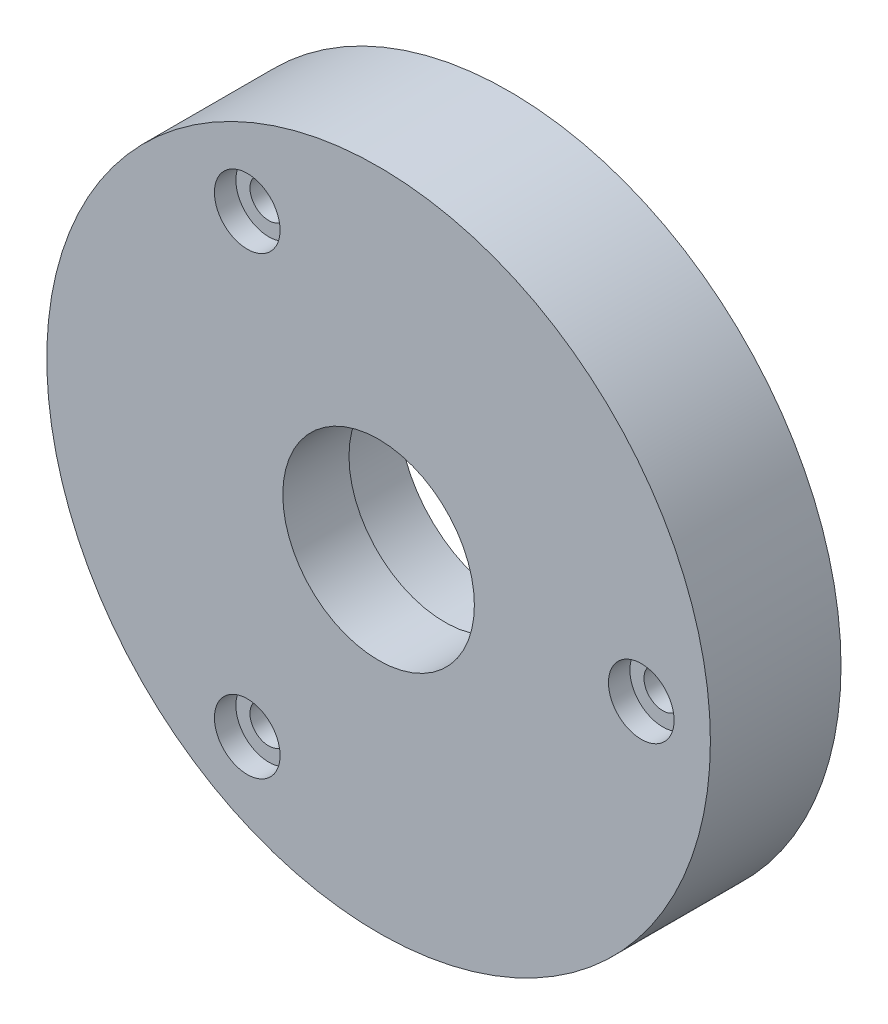
SolidWorks part; units mm, degrees
material "Alliage 1060"
ref_plane "Plan de face" through (0, 0, 0) normal (0, 0, 1) x (1, 0, 0)
ref_plane "Plan de dessus" through (0, 0, 0) normal (0, 1, 0) x (1, 0, 0)
ref_plane "Plan de droite" through (0, 0, 0) normal (1, 0, 0) x (0, 0, -1)
sketch "Esquisse1" plane through (0, 0, 0) normal (0, 0, 1) x (1, 0, 0)
  circle A2 centre (23.0123, 8.4359) radius 38.1
  circle A3 centre (23.0123, 8.4359) radius 11
  dimension "D1" = 76.2
  dimension "D2" = 22
extrude "Boss.-Extru.1" add sketch "Esquisse1" along normal blind 15
sketch "Esquisse2" plane through (0, 0, 0) normal (0, 0, -1) x (-1, 0, 0)
  circle A0 centre (-23.0123, 8.4359) radius 12.7
  dimension "D1" = 25.4
extrude "Enlèv. mat.-Extru.1" cut sketch "Esquisse2" against normal blind 7.4
sketch "Esquisse3" plane through (0, 0, 15) normal (0, 0, 1) x (1, 0, 0)
  line L0 (-15.0877, 8.4359) -> (61.1123, 8.4359) construction
  circle A0 centre (23.0123, 8.4359) radius 38.1 construction
  circle A1 centre (53.1748, 8.4359) radius 1.8
  circle A2 centre (7.931, -17.6856) radius 1.8
  circle A3 centre (7.931, 34.5574) radius 1.8
  point P7 (23.0123, 8.4359)
  point P12 (23.0123, 8.4359)
  dimension "D1" = 3.6
  dimension "D2" = 30.1625
  dimension "D3" = 3
hole_wizard "Chambrage pour vis à tête ronde bombée #61" positions "Esquisse4" profile "Esquisse5" counterbore size "#6" standard "Ansi Inch"
sketch "Esquisse4" plane through (0, 0, 15) normal (0, 0, 1) x (1, 0, 0)
  point P0 (7.931, 34.5574)
  point P3 (53.1748, 8.4359)
  point P6 (7.931, -17.6856)
sketch "Esquisse5" plane through (7.931, 34.5574, 15) normal (1, 0, 0) x (0, -1, 0)
  line L0 (0, 0) -> (0, 16.2934)
  line L1 (0, 16.2934) -> (2.1526, 15)
  line L2 (2.1526, 15) -> (2.1526, 2.4638)
  line L3 (2.1526, 2.4638) -> (3.7706, 2.4638)
  line L4 (3.7706, 2.4638) -> (3.7706, 0)
  line L5 (3.7706, 0) -> (0, 0)
  line L10 (0, 16.2934) -> (-2.1527, 15) construction
  line L11 (0, -6.35) -> (0, 107.95) construction
  dimension "Diamètre du perçage" = 4.3053
  dimension "Profondeur du perçage" = 15
  dimension "Diamètre du chambrage" = 7.5413
  dimension "Profondeur du chambrage" = 2.4638
  dimension "Angle de pointe" = 118
sketch "Esquisse6" plane through (0, 0, 0) normal (0, 0, -1) x (-1, 0, 0)
  line L0 (-23.0123, 8.4359) -> (-23.0123, 40.1859) construction
  line L1 (-23.0123, 8.4359) -> (-33.8714, -21.3994) construction
  dimension "D1" = 31.75
hole_wizard "1/8 (0.124) Trous de centrage1" positions "Esquisse8" profile "Esquisse9" hole size "1/8" standard "Ansi Inch"
sketch "Esquisse8" plane through (0, 0, 0) normal (0, 0, -1) x (-1, 0, 0)
  point P0 (-23.0123, 40.1859)
  point P3 (-33.8714, -21.3994)
sketch "Esquisse9" plane through (23.0123, 40.1859, 0) normal (1, 0, 0) x (0, 1, 0)
  line L0 (0, 0) -> (0, 7.2962)
  line L1 (0, 7.2962) -> (1.5748, 6.35)
  line L2 (1.5748, 6.35) -> (1.5748, 0)
  line L5 (1.5748, 0) -> (0, 0)
  line L10 (0, 7.2962) -> (-1.5748, 6.35) construction
  line L11 (0, -6.35) -> (0, 107.95) construction
  dimension "Diamètre du perçage" = 3.1496
  dimension "Profondeur du perçage" = 6.35
  dimension "Angle de pointe" = 118
